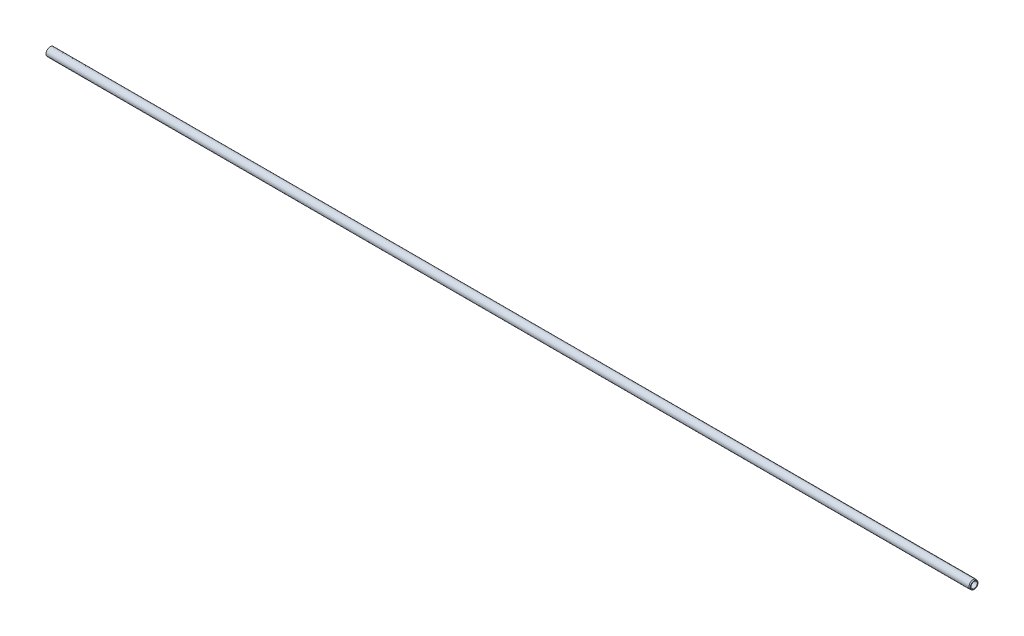
SolidWorks part; units mm, degrees
ref_plane "Front" through (0, 0, 0) normal (0, 0, 1) x (1, 0, 0)
ref_plane "Top" through (0, 0, 0) normal (0, 1, 0) x (1, 0, 0)
ref_plane "Right" through (0, 0, 0) normal (1, 0, 0) x (0, 0, -1)
sketch "Sketch1" plane through (0, 0, 0) normal (0, 0, 1) x (1, 0, 0)
  line L0 (0, 0) -> (1352.4571, 0) construction
  line L1 (0, 10) -> (0, 7.5)
  line L2 (0, 7.5) -> (2208, 7.5)
  line L4 (0, 10) -> (2205.5, 10)
  line L6 (2205.5, 10) -> (2208, 9.0901)
  line L7 (2208, 9.0901) -> (2208, 7.5)
  dimension "D1" = 2.5
  dimension "D2" = 15
  dimension "D3" = 20
  dimension "D4" = 20
  dimension "D6" = 2208
revolve "Base-Revolve" add sketch "Sketch1" angle 360 about L0
